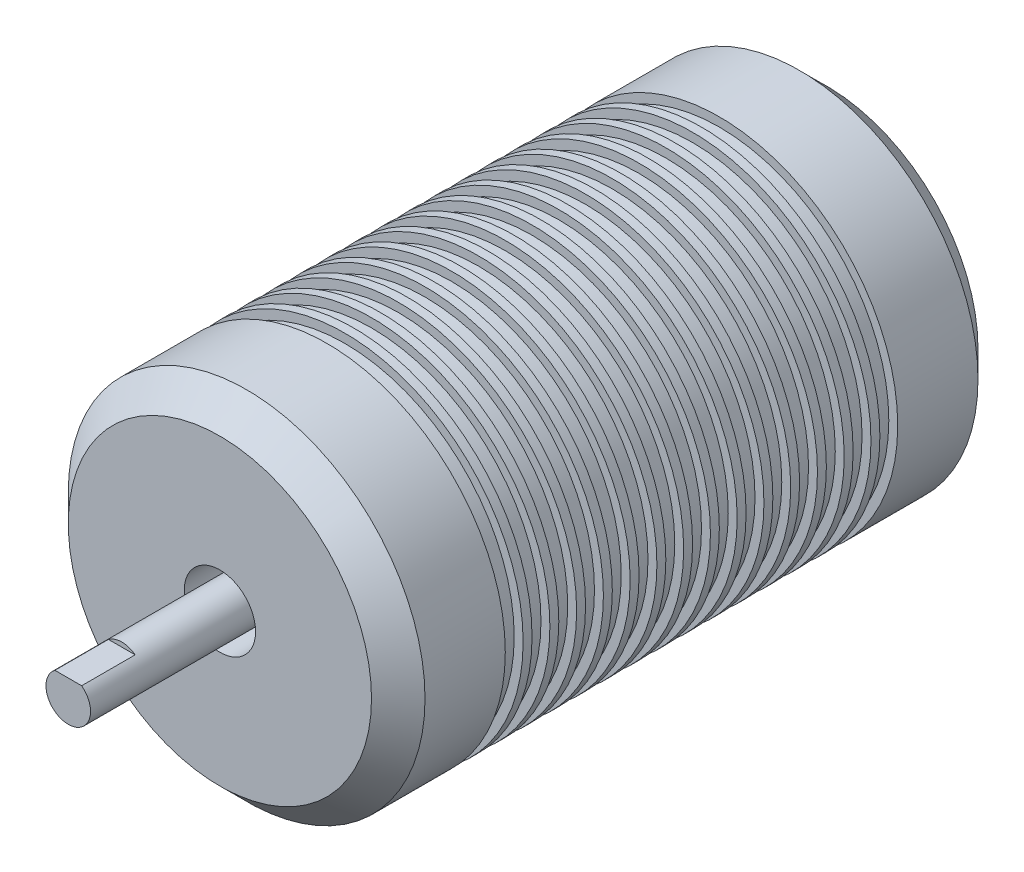
SolidWorks part; units mm, degrees
material "6061-T6 (SS)"
ref_plane "Front Plane" through (0, 0, 0) normal (0, 0, 1) x (1, 0, 0)
ref_plane "Top Plane" through (0, 0, 0) normal (0, 1, 0) x (1, 0, 0)
ref_plane "Right Plane" through (0, 0, 0) normal (1, 0, 0) x (0, 0, -1)
sketch "Sketch1" plane through (0, 0, 0) normal (0, 0, 1) x (1, 0, 0)
  circle A0 centre (0, 0) radius 20
  dimension "D1" = 40
extrude "Boss-Extrude1" add sketch "Sketch1" along normal blind 68
sketch "Sketch2" plane through (0, 0, 68) normal (0, 0, 1) x (1, 0, 0)
  circle A0 centre (0, 0) radius 2.5 construction
  circle A1 centre (0, 0) radius 4
  dimension "D1" = 5
  dimension "D2" = 1.5
extrude "Cut-Extrude1" cut sketch "Sketch2" against normal blind 10
sketch "Sketch3" plane through (0, 0, 58) normal (0, 0, 1) x (1, 0, 0)
  circle A0 centre (0, 0) radius 2.5
  dimension "D1" = 5
extrude "Boss-Extrude2" add sketch "Sketch3" along normal blind 27
sketch "Sketch4" plane through (0, 0, 85) normal (0, 0, 1) x (1, 0, 0)
  line L0 (-1.5, 2) -> (1.5, 2)
  circle A0 centre (0, 0) radius 2.5 construction
  circle A1 centre (0, 0) radius 2.5
  point P3 (0, 2.5)
  circle M2 centre (0, 0) radius 2.5
  dimension "D1" = 0.5
extrude "Cut-Extrude2" cut sketch "Sketch4" against normal blind 6 contours L0 M2
chamfer "Chamfer1" distance 3 angle 45 2 edges at (20, 0, 0) (20, 0, 68)
sketch3d "3DSketch1"
  line L0 (0, 0, 68) -> (0, 0, 0)
  circle A0 centre (0, 0, 0) radius 17 construction
  circle A1 centre (0, 0, 68) radius 17 construction
  circle A2 centre (0, 0, 0) radius 17
  circle A3 centre (0, 0, 68) radius 17
  point P2 (0, 0, -17)
  point P5 (0, 0, 85)
  point P7 (0, 0, -17)
  point P9 (0, 0, 85)
sketch "Sketch5" plane through (0, 0, 68) normal (0, 0, 1) x (1, 0, 0)
  circle A0 centre (0, 0) radius 19
  circle A1 centre (0, 0) radius 20 construction
  circle A2 centre (0, 0) radius 20
  dimension "D1" = 1
extrude "Cut-Extrude3" cut sketch "Sketch5" against normal blind 2 from offset 12 offset against normal yes
pattern_linear "LPattern1" count 15 spacing 3 along (0, 0, -1) of "Cut-Extrude3"
